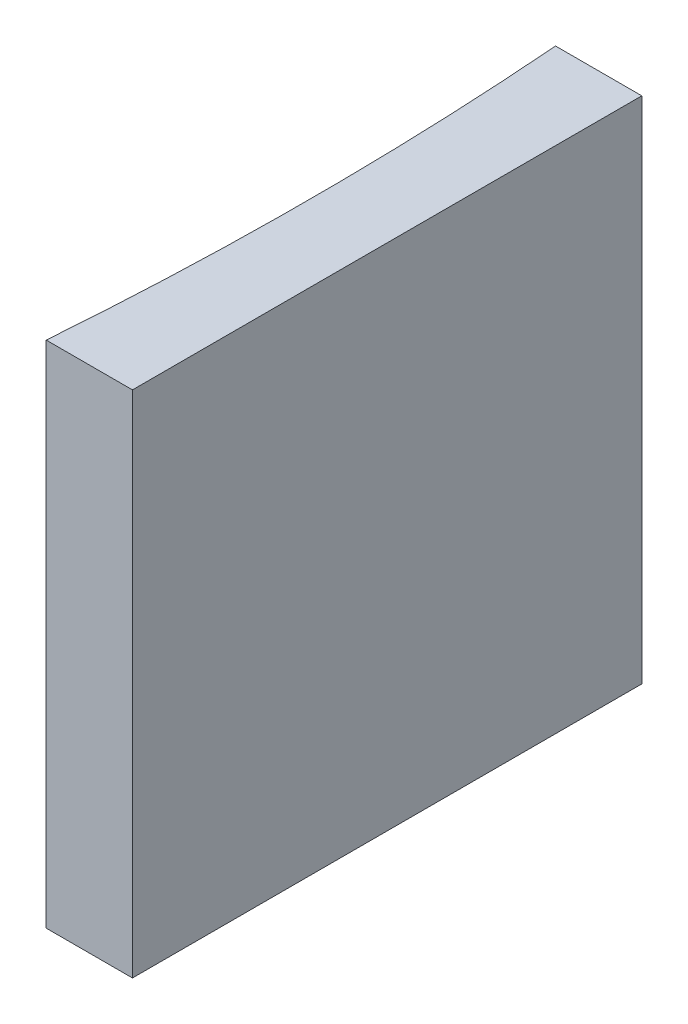
SolidWorks part; units mm, degrees
ref_plane "前视基准面" through (0, 0, 0) normal (0, 0, 1) x (1, 0, 0)
ref_plane "上视基准面" through (0, 0, 0) normal (0, 1, 0) x (1, 0, 0)
ref_plane "右视基准面" through (0, 0, 0) normal (1, 0, 0) x (0, 0, -1)
sketch "草图1" plane through (0, 0, 0) normal (0, 1, 0) x (1, 0, 0)
  line L0 (0, 0) -> (0, -20)
  line L1 (0, 0) -> (-3.3874, 0)
  line L2 (0, -20) -> (-3.3874, -20)
  line L3 (8.2336, -10) -> (-10.4405, -10) construction
  arc A0 (-3.3874, -20) -> (-3.3874, 0) centre (-132.25, -10) ccw
  point P7 (-3, -10)
  point P8 (0, -10)
  dimension "D2" = 129.25
  dimension "D3" = 3
  dimension "D1" = 20
extrude "凸台-拉伸1" add sketch "草图1" along normal blind 20
